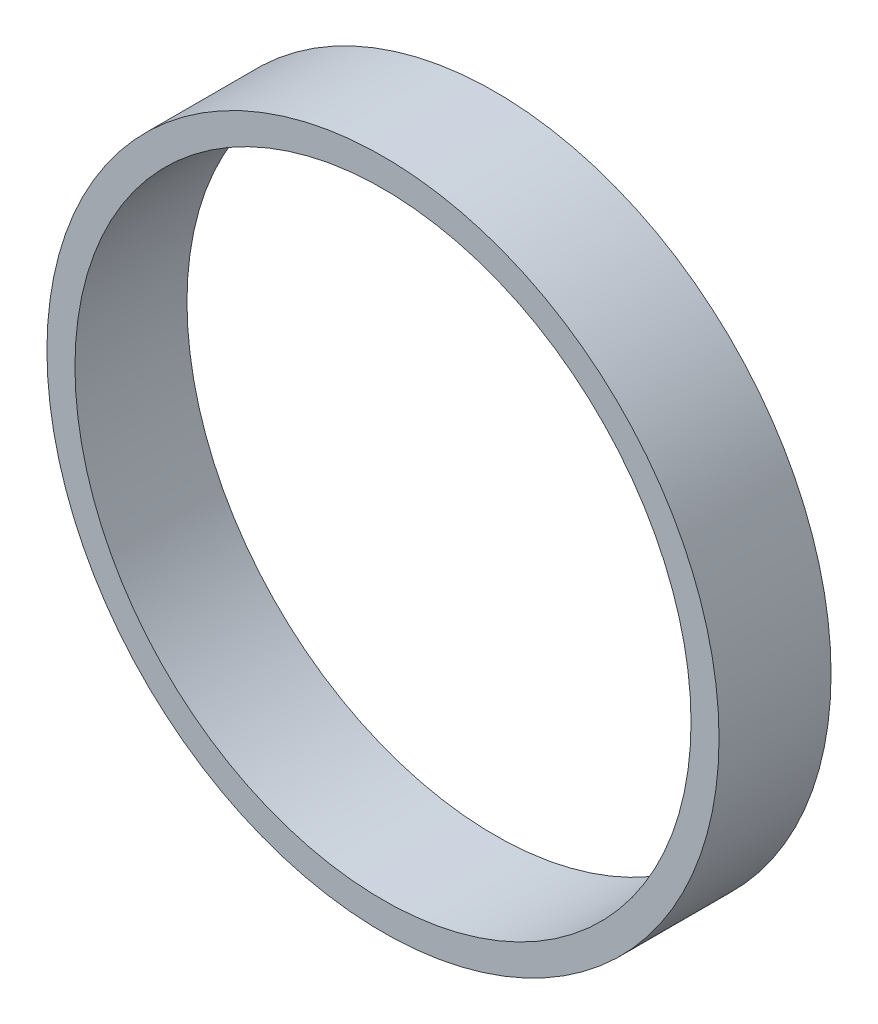
SolidWorks part; units mm, degrees
ref_plane "前视基准面" through (0, 0, 0) normal (0, 0, 1) x (1, 0, 0)
ref_plane "上视基准面" through (0, 0, 0) normal (0, 1, 0) x (1, 0, 0)
ref_plane "右视基准面" through (0, 0, 0) normal (1, 0, 0) x (0, 0, -1)
other "Configuration Table"
sketch "草图1" plane through (0, 0, 0) normal (0, 0, 1) x (1, 0, 0)
  circle A0 centre (0, 0) radius 27.5
  circle A1 centre (0, 0) radius 30
extrude "凸台-拉伸1" add sketch "草图1" along normal blind 10
